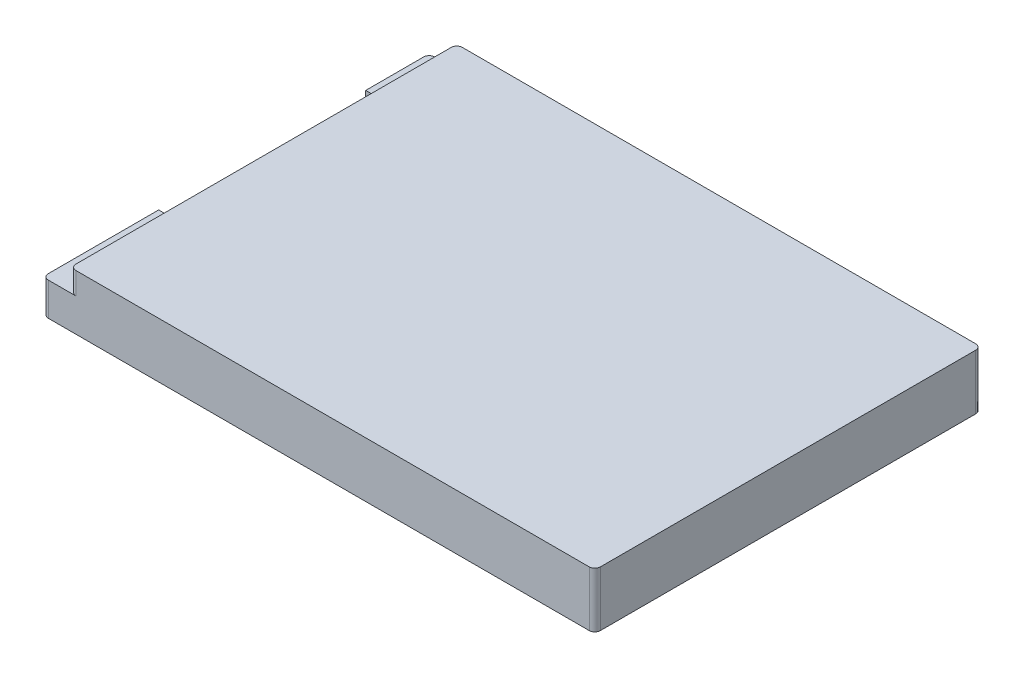
SolidWorks part; units mm, degrees
material "1060 Alloy"
ref_plane "Front Plane" through (0, 0, 0) normal (0, 0, 1) x (1, 0, 0)
ref_plane "Top Plane" through (0, 0, 0) normal (0, 1, 0) x (1, 0, 0)
ref_plane "Right Plane" through (0, 0, 0) normal (1, 0, 0) x (0, 0, -1)
sketch "Sketch1" plane through (0, 0, 0) normal (0, 1, 0) x (1, 0, 0)
  line L1 (0, 0) -> (100, 0)
  line L2 (0, 0) -> (0, 70)
  line L3 (0, 70) -> (100, 70)
  line L4 (100, 0) -> (100, 70)
  dimension "D1" = 100
  dimension "D2" = 70
extrude "Boss-Extrude1" add sketch "Sketch1" along normal blind 10
sketch "Sketch2" plane through (0, 0, 0) normal (0, -1, 0) x (1, 0, 0)
  line L1 (0, -70) -> (100, -70) construction
  line L2 (0, -70) -> (0, 0) construction
  line L3 (0, 0) -> (100, 0) construction
  line L4 (100, -70) -> (100, 0) construction
  line L5 (14, -66) -> (91, -66) construction
  line L6 (14, -66) -> (14, -4) construction
  line L7 (14, -4) -> (91, -4) construction
  line L8 (91, -66) -> (91, -4) construction
  circle A0 centre (14, -4) radius 1.5
  circle A1 centre (14, -66) radius 1.5
  circle A2 centre (91, -66) radius 1.5
  circle A3 centre (91, -4) radius 1.5
  dimension "D5" = 3
  dimension "D1" = 14
  dimension "D2" = 9
  dimension "D3" = 4
  dimension "D4" = 4
extrude "Cut-Extrude1" cut sketch "Sketch2" against normal blind 5
sketch "Sketch3" plane through (0, 0, 0) normal (-1, 0, 0) x (0, 0, 1)
  line L0 (-70, 6) -> (-70, 10)
  line L1 (-70, 10) -> (-70, 0) construction
  line L2 (-70, 10) -> (0, 10)
  line L3 (0, 10) -> (0, 6)
  line L4 (0, 10) -> (0, 0) construction
  line L5 (0, 6) -> (-21, 6)
  line L6 (-21, 6) -> (-21, 0)
  line L7 (-70, 0) -> (0, 0) construction
  line L8 (-21, 0) -> (-58.5, 0)
  line L9 (-58.5, 0) -> (-58.5, 6)
  line L10 (-58.5, 6) -> (-70, 6)
  line L12 (-54.6009, 4.3477) -> (-37.0191, 4.3477)
  line L13 (-54.6009, 4.3477) -> (-54.6009, 3.2915)
  line L14 (-54.6009, 3.2915) -> (-37.0191, 3.2915)
  line L15 (-37.0191, 4.3477) -> (-37.0191, 3.2915)
  line L16 (-33.54, 4.3477) -> (-24.5317, 4.3477)
  line L17 (-33.54, 4.3477) -> (-33.54, 3.2915)
  line L18 (-33.54, 3.2915) -> (-24.5317, 3.2915)
  line L19 (-24.5317, 4.3477) -> (-24.5317, 3.2915)
  dimension "D1" = 11.5
  dimension "D2" = 6
  dimension "D3" = 21
extrude "Cut-Extrude2" cut sketch "Sketch3" against normal blind 5
fillet "Fillet1" radius 1 6 edges at (100, 5, -70) (100, 5, 0) (5, 8, 0) (0, 3, 0) (5, 8, -70) (0, 3, -70)
